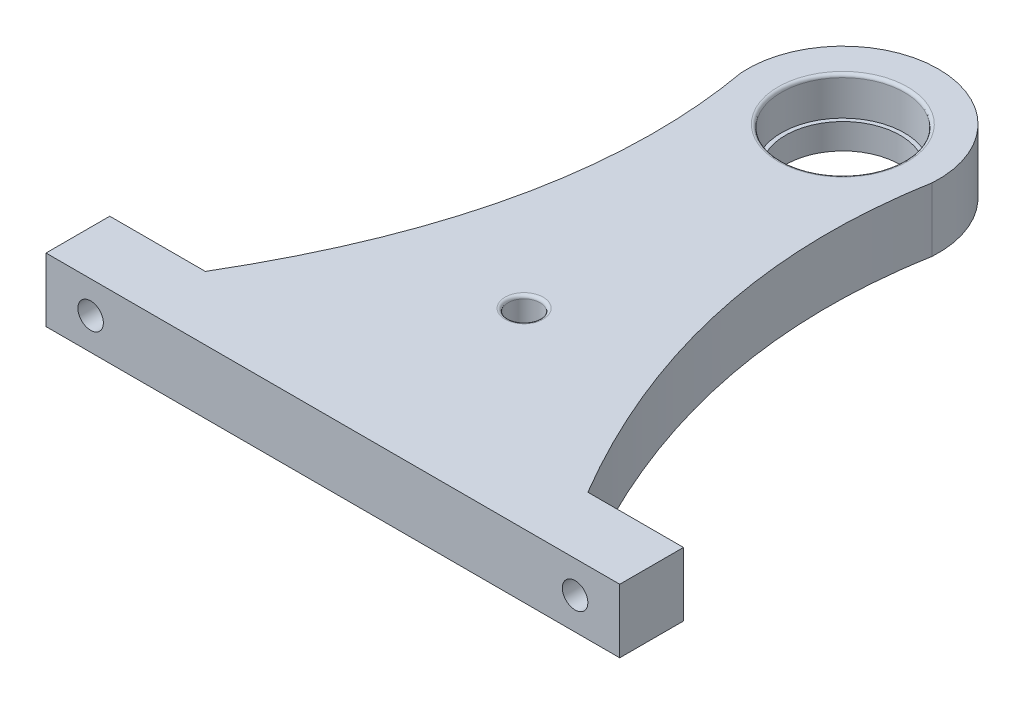
SolidWorks part; units mm, degrees
ref_plane "Спереди" through (0, 0, 0) normal (0, 0, 1) x (1, 0, 0)
ref_plane "Сверху" through (0, 0, 0) normal (0, 1, 0) x (1, 0, 0)
ref_plane "Справа" through (0, 0, 0) normal (1, 0, 0) x (0, 0, -1)
sketch "Эскиз1" plane through (0, 0, 0) normal (0, 1, 0) x (1, 0, 0)
  line L0 (0, 42.9636) -> (0, -37.0364) construction
  line L1 (31.2466, -22.0364) -> (-63.8578, -22.0364) construction
  line L2 (-28.6541, -37.0364) -> (31.2466, -37.0364) construction
  line L3 (-45, -37.0364) -> (45, -37.0364)
  line L4 (45, -37.0364) -> (45, -27.0364)
  line L5 (45, -27.0364) -> (30, -27.0364)
  line L6 (0, 42.9636) -> (0, 72.4932) construction
  line L7 (-45, -37.0364) -> (-45, -27.0364)
  line L8 (-45, -27.0364) -> (-30, -27.0364)
  arc A0 (14.9684, 41.9907) -> (-14.9684, 41.9907) centre (0, 42.9636) ccw
  spline S0 degree 2 poles (30, -27.0364) (8.9822, 8.4827) (14.9684, 41.9907) knots 0 0 0 0.673052 0.673052 0.673052
  spline S1 degree 2 poles (-30, -27.0364) (-8.9822, 8.4827) (-14.9684, 41.9907) knots 0 0 0 0.673052 0.673052 0.673052
  dimension "D1" = 30
  dimension "D2" = 80
  dimension "D3" = 45
  dimension "D4" = 15
  dimension "D5" = 10
extrude "Бобышка-Вытянуть1" add sketch "Эскиз1" along normal blind 10
sketch "Эскиз2" plane through (0, 10, 0) normal (0, 1, 0) x (1, 0, 0)
  circle A0 centre (0, 42.9636) radius 9.65
  dimension "D1" = 19.3
extrude "Вырез-Вытянуть1" cut sketch "Эскиз2" against normal blind 6
sketch "Эскиз3" plane through (0, 4, 0) normal (0, 1, 0) x (1, 0, 0)
  circle A0 centre (0, 42.9636) radius 9
  dimension "D1" = 18
extrude "Вырез-Вытянуть2" cut sketch "Эскиз3" against normal through all
sketch "Эскиз4" plane through (0, 0, 27.0364) normal (0, 0, -1) x (-1, 0, 0)
  line L0 (30, 0) -> (45, 0) construction
  line L1 (45, 10) -> (45, 0) construction
  line L2 (-45, 10) -> (-45, 0) construction
  line L3 (-45, 0) -> (-30, 0) construction
  circle A0 centre (38, 5) radius 2
  circle A1 centre (-38, 5) radius 2
  point P8 (-45, 5)
  dimension "D2" = 7
  dimension "D3" = 4
  dimension "D4" = 7
  dimension "D1" = 5
  dimension "D5" = 5
extrude "Вырез-Вытянуть3" cut sketch "Эскиз4" against normal through all
sketch "Эскиз5" plane through (0, 10, 0) normal (0, 1, 0) x (1, 0, 0)
  circle A0 centre (0, -7.0364) radius 2.5
  circle A1 centre (0, 42.9636) radius 9.65 construction
  dimension "D1" = 5
  dimension "D2" = 50
extrude "Вырез-Вытянуть4" cut sketch "Эскиз5" against normal blind 8
fillet "Скругление1" radius 0.5 1 edges at (0, 10, 9.5364)
fillet "Скругление2" radius 0.5 1 edges at (0, 10, -33.3136)
